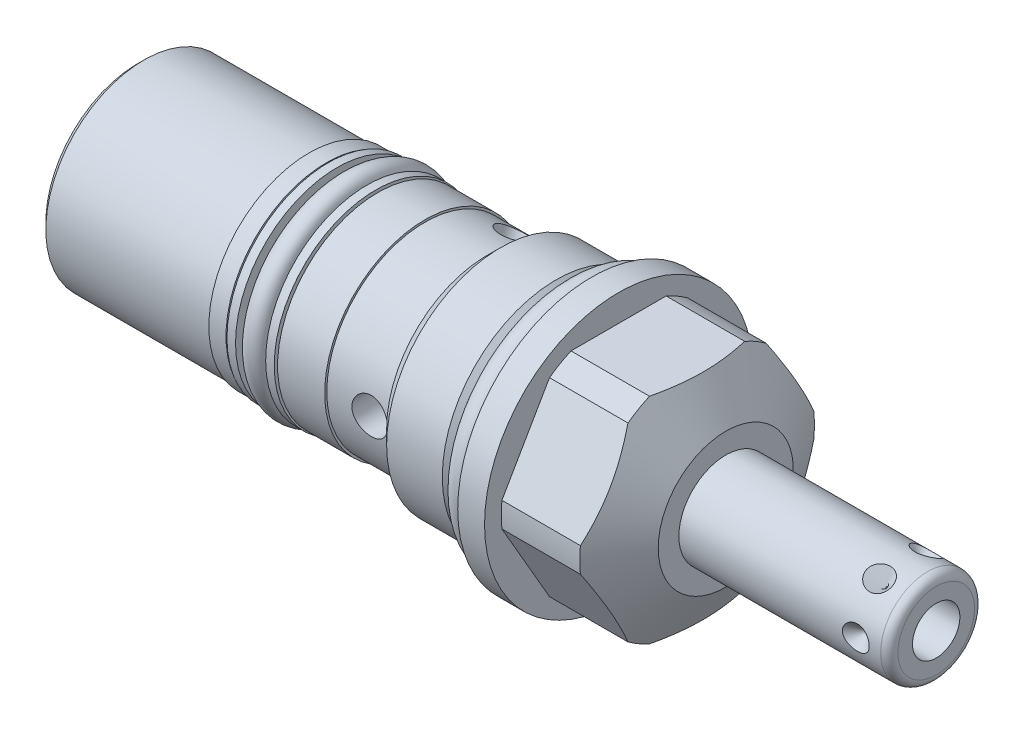
SolidWorks part; units mm, degrees
material "Alloy Steel"
ref_plane "Front Plane" through (0, 0, 0) normal (0, 0, 1) x (1, 0, 0)
ref_plane "Top Plane" through (0, 0, 0) normal (0, 1, 0) x (1, 0, 0)
ref_plane "Right Plane" through (0, 0, 0) normal (1, 0, 0) x (0, 0, -1)
sketch "Sketch1" plane through (0, 0, 0) normal (0, 0, 1) x (1, 0, 0)
  line L0 (0, 0) -> (113.8544, 0) construction
  line L1 (0, 15.875) -> (3.175, 15.875)
  line L2 (3.175, 15.875) -> (3.175, 13.8938)
  line L3 (3.175, 13.8938) -> (12.4728, 13.8938)
  line L4 (12.4728, 13.8938) -> (15.875, 8.001)
  line L5 (15.875, 8.001) -> (15.875, 0)
  line L6 (15.875, 0) -> (-53.7972, 0)
  line L7 (-53.7972, 0) -> (-53.7972, 11.6205)
  line L8 (0, 15.875) -> (0, 12.0015)
  line L9 (0, 12.0015) -> (-2.7178, 12.0015)
  line L10 (-2.7178, 12.0015) -> (-4.21, 13.4937)
  line L11 (-4.21, 13.4937) -> (-10.8013, 13.4937)
  line L12 (-10.8013, 13.4937) -> (-12.4206, 11.8745)
  line L14 (-12.4206, 11.8745) -> (-12.4206, 11.6205)
  line L15 (-12.4206, 11.6205) -> (-53.7972, 11.6205)
  dimension "D1" = 31.75
  dimension "D2" = 16.002
  dimension "D3" = 3.175
  dimension "D4" = 15.875
  dimension "D5" = 27.7876
  dimension "D6" = 30
  dimension "D7" = 53.7972
  dimension "D8" = 51.0794
  dimension "D9" = 24.003
  dimension "D10" = 45
  dimension "D11" = 26.9875
  dimension "D12" = 9.7028
  dimension "D13" = 23.749
  dimension "D14" = 23.241
revolve "Revolve1" add sketch "Sketch1" angle 360 about L0
sketch "Sketch2" plane through (15.875, 0, 0) normal (1, 0, 0) x (0, 0, -1)
  line L1 (7.3323, 12.7) -> (-7.3323, 12.7)
  line L2 (-7.3323, 12.7) -> (-14.6647, 0)
  line L3 (-14.6647, 0) -> (-7.3323, -12.7)
  line L4 (-7.3323, -12.7) -> (7.3323, -12.7)
  line L5 (7.3323, -12.7) -> (14.6647, 0)
  line L6 (14.6647, 0) -> (7.3323, 12.7)
  circle A0 centre (0, 0) radius 12.7 construction
  dimension "D1" = 25.4
extrude "Cut-Extrude1" cut sketch "Sketch2" against normal up to surface (12.7 mm away) flip side to cut up to face at (3.175, 0, 15.875)
sketch "Sketch3" plane through (0, 0, 0) normal (0, 0, 1) x (1, 0, 0)
  line L0 (0, 0) -> (52.5154, 0) construction
  line L1 (15.875, 5.5563) -> (39.7764, 5.5562)
  line L2 (15.875, -8.001) -> (15.875, 8.001) construction
  line L3 (40.7924, 4.5402) -> (40.7924, 0)
  line L4 (40.7924, 0) -> (15.875, 0)
  line L5 (15.875, 0) -> (15.875, 5.5563)
  line L6 (0, 15.875) -> (0, -15.875) construction
  arc A0 (40.7924, 4.5402) -> (39.7764, 5.5562) centre (39.7764, 4.5402) ccw
  dimension "D1" = 1.016
  dimension "D2" = 40.7924
  dimension "D3" = 11.1125
revolve "Revolve2" add sketch "Sketch3" angle 360 about L0
sketch "Sketch4" plane through (0, 0, 0) normal (0, 1, 0) x (1, 0, 0)
  line L0 (36.83, 10.0738) -> (36.83, 0) construction
  line L1 (40.7924, -4.5402) -> (40.7924, 4.5402) construction
  line L2 (38.4175, 5.5563) -> (36.83, 5.5563)
  line L3 (39.7764, 5.5563) -> (15.875, 5.5563) construction
  line L4 (36.83, 5.5563) -> (36.83, 3.9687)
  line L5 (36.83, 3.9687) -> (38.4175, 5.5563)
  dimension "D1" = 3.9624
  dimension "D2" = 45
  dimension "D3" = 3.175
revolve "Cut-Revolve1" cut sketch "Sketch4" angle 360 about L0
pattern_circular "CirPattern1" count 6 over 360 about axis through (0, 0, 0) along (-1, 0, 0) of "Cut-Revolve1"
sketch "Sketch5" plane through (0, 0, 0) normal (0, 0, 1) x (1, 0, 0)
  line L0 (0, 0) -> (44.9273, 0) construction
  line L1 (40.7924, 2.8067) -> (30.6324, 2.8067)
  line L2 (40.7924, -4.5402) -> (40.7924, 4.5402) construction
  line L3 (30.6324, 2.8067) -> (28.946, 0)
  line L4 (28.946, 0) -> (40.7924, 0)
  line L5 (40.7924, 0) -> (40.7924, 2.8067)
  dimension "D1" = 10.16
  dimension "D2" = 59
  dimension "D3" = 5.6134
revolve "Cut-Revolve2" cut sketch "Sketch5" angle 360 about L0
sketch "Sketch6" plane through (0, 0, 0) normal (0, 0, 1) x (1, 0, 0)
  line L0 (-19.7612, 11.6205) -> (-19.7612, 11.8745)
  line L1 (-12.4206, 11.6205) -> (-53.7972, 11.6205) construction
  line L2 (-19.7612, 11.8745) -> (-33.4772, 11.8745)
  line L3 (-33.4772, 11.8745) -> (-33.4772, 11.6205)
  line L4 (-33.4772, 11.6205) -> (-19.7612, 11.6205)
  line L5 (0, 0) -> (-62.9111, 0) construction
  line L6 (-53.7972, 11.6205) -> (-53.7972, -11.6205) construction
  dimension "D1" = 13.716
  dimension "D2" = 23.749
  dimension "D3" = 20.32
revolve "Revolve3" add sketch "Sketch6" angle 360 about L5
sketch "Sketch7" plane through (-53.7972, 0, 0) normal (-1, 0, 0) x (0, 0, 1)
  circle A0 centre (0, 0) radius 0.8001
  dimension "D1" = 1.6002
extrude "Cut-Extrude2" cut sketch "Sketch7" against normal blind 0.762
sketch "Sketch8" plane through (0, 0, 0) normal (0, 0, 1) x (1, 0, 0)
  line L0 (0, 0) -> (-56.7277, 0) construction
  line L1 (-19.7612, 11.8745) -> (-33.4772, 11.8745) construction
  line L2 (-31.4452, 11.8745) -> (-25.3365, 11.8745)
  line L3 (-31.4452, 11.8745) -> (-31.4452, 9.8298)
  line L4 (-31.4452, 9.8298) -> (-25.3365, 9.8298)
  line L5 (-25.3365, 11.8745) -> (-25.3365, 9.8298)
  line L6 (-53.7972, 11.6205) -> (-53.7972, -11.6205) construction
  dimension "D1" = 6.1087
  dimension "D2" = 22.352
  dimension "D3" = 19.6596
revolve "Cut-Revolve3" cut sketch "Sketch8" angle 360 about L0
sketch "Sketch9" plane through (0, 0, 0) normal (0, 0, 1) x (1, 0, 0)
  line L0 (0, 0) -> (-59.2046, 0) construction
  line L1 (-28.3908, 14.9069) -> (-28.3908, -14.8344) construction
  line L2 (-31.4452, -11.8745) -> (-31.4452, 11.8745) construction
  line L3 (-25.3365, 9.8298) -> (-25.3365, -9.8298) construction
  line L4 (-25.3365, 9.8298) -> (-31.4452, 9.8298) construction
  line L5 (-26.6065, 12.0142) -> (-25.5905, 12.0142)
  line L6 (-26.6065, 12.0142) -> (-26.6065, 9.8298)
  line L7 (-26.6065, 9.8298) -> (-25.5905, 9.8298)
  line L8 (-25.5905, 12.0142) -> (-25.5905, 9.8298)
  line L9 (-25.3365, 11.8745) -> (-25.3365, -11.8745) construction
  line L10 (-31.1912, 12.0142) -> (-31.1912, 9.8298)
  line L11 (-30.1752, 9.8298) -> (-31.1912, 9.8298)
  line L12 (-30.1752, 12.0142) -> (-30.1752, 9.8298)
  line L13 (-30.1752, 12.0142) -> (-31.1912, 12.0142)
  dimension "D1" = 1.016
  dimension "D2" = 0.254
  dimension "D3" = 2.1844
revolve "Revolve4" add sketch "Sketch9" angle 360 about L0
sketch "Sketch10" plane through (0, 0, 0) normal (0, 1, 0) x (1, 0, 0)
  line L0 (-14.6812, 23.0369) -> (-14.6812, -3.4735) construction
  line L1 (-53.7972, 11.6205) -> (-53.7972, -11.6205) construction
  line L2 (-14.6812, -11.6205) -> (-16.7894, -11.6205)
  line L4 (-16.7894, -11.6205) -> (-16.7894, -0.7937)
  line L5 (-16.7894, -0.7937) -> (-14.6812, -0.7937)
  line L6 (-14.6812, -0.7937) -> (-14.6812, -11.6205)
  line L7 (-19.7612, -11.6205) -> (-12.4206, -11.6205) construction
  dimension "D1" = 39.116
  dimension "D2" = 4.2164
  dimension "D3" = 0.7937
revolve "Cut-Revolve4" cut sketch "Sketch10" angle 360 about L0
pattern_circular "CirPattern2" count 3 over 360 about axis through (0, 0, 0) along (1, 0, 0) of "Cut-Revolve4"
chamfer "Chamfer1" distance 0.762 angle 45 1 edges at (-53.7972, 0, 11.6205)
sketch "Sketch11" plane through (0, 0, 0) normal (0, 0, 1) x (1, 0, 0)
  line L0 (0, 0) -> (23.6366, 0) construction
  line L1 (0, 15.875) -> (0, -15.875) construction
  line L2 (0, 12.0015) -> (-2.7178, 12.0015) construction
  circle A0 centre (-1.4732, 13.4747) radius 1.4732
  dimension "D1" = 2.9464
  dimension "D2" = 26.9494
revolve "Revolve5" add sketch "Sketch11" angle 360 about L0
sketch "Sketch12" plane through (0, 0, 0) normal (0, 0, 1) x (1, 0, 0)
  line L0 (0, 0) -> (-56.0967, 0) construction
  line L1 (-26.6065, 9.8298) -> (-30.1752, 9.8298) construction
  line L2 (-28.3908, 11.1379) -> (-28.3908, 6.0377) construction
  line L3 (-31.4452, -11.8745) -> (-31.4452, 11.8745) construction
  line L4 (-25.3365, 9.8298) -> (-25.3365, -9.8298) construction
  circle A0 centre (-28.3908, 11.1379) radius 1.3081
  dimension "D1" = 2.6162
revolve "Revolve7" add sketch "Sketch12" angle 360 about L0
